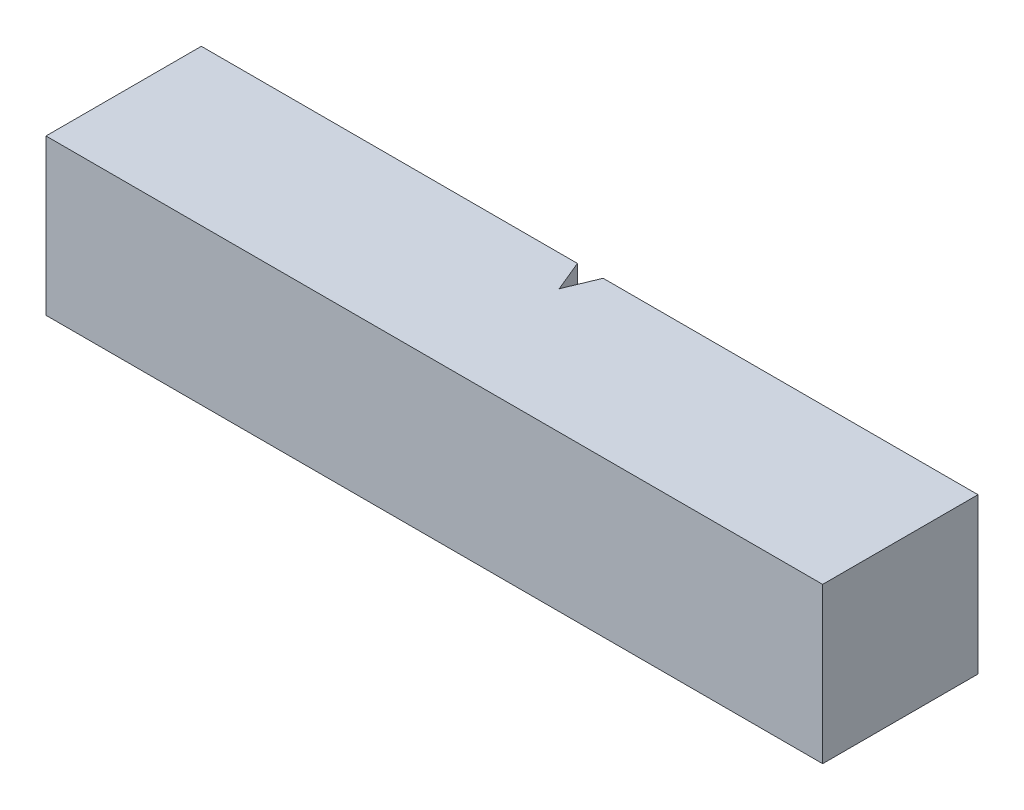
SolidWorks part; units mm, degrees
ref_plane "Front Plane" through (0, 0, 0) normal (0, 0, 1) x (1, 0, 0)
ref_plane "Top Plane" through (0, 0, 0) normal (0, 1, 0) x (1, 0, 0)
ref_plane "Right Plane" through (0, 0, 0) normal (1, 0, 0) x (0, 0, -1)
sketch "Sketch1" plane through (0, 0, 0) normal (0, 1, 0) x (1, 0, 0)
  line L0 (-31.7, 12.7) -> (-31.7, 0) construction
  line L1 (0, 0) -> (-63.5, 0)
  line L2 (0, 0) -> (0, 12.7)
  line L3 (0, 12.7) -> (-63.5, 12.7)
  line L4 (-63.5, 0) -> (-63.5, 12.7)
  line L5 (-32.7521, 12.7) -> (-31.7, 10.16)
  line L6 (-31.7, 10.16) -> (-30.6479, 12.7)
  dimension "D1" = 12.7
  dimension "D2" = 63.5
  dimension "D3" = 10.16
  dimension "D4" = 31.8
  dimension "D5" = 22.5
  dimension "D6" = 22.5
extrude "Boss-Extrude1" add sketch "Sketch1" along normal blind 12.7 contours L0 L5 L3 L4 L1 | L6 L0 L1 L2 L3
